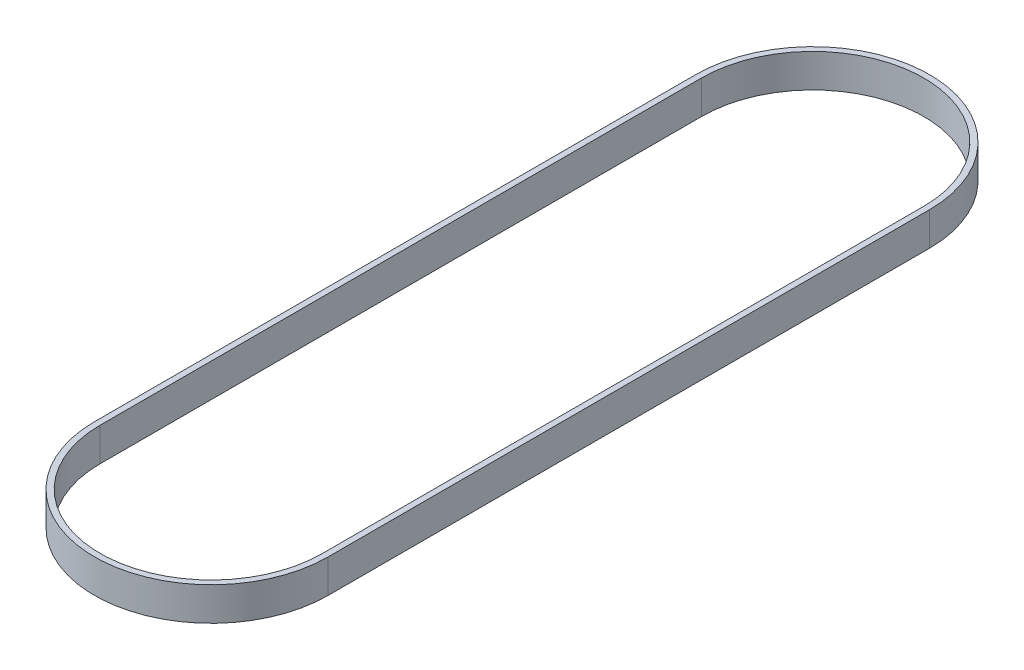
SolidWorks part; units mm, degrees
material "聚亚安酯(11671)"
ref_plane "前视基准面" through (0, 0, 0) normal (0, 0, 1) x (1, 0, 0)
ref_plane "上视基准面" through (0, 0, 0) normal (0, 1, 0) x (1, 0, 0)
ref_plane "右视基准面" through (0, 0, 0) normal (1, 0, 0) x (0, 0, -1)
sketch "草图1" plane through (0, 0, 0) normal (0, 1, 0) x (1, 0, 0)
  line L0 (0, -90) -> (0, 90) construction
  line L2 (-35, 90) -> (-35, -90)
  line L4 (35, 90) -> (35, -90)
  line L6 (-33.26, 90) -> (-33.26, -90)
  line L8 (33.26, -90) -> (33.26, 90)
  arc A0 (33.26, 90) -> (-33.26, 90) centre (0, 90) ccw
  arc A1 (-33.26, -90) -> (33.26, -90) centre (0, -90) ccw
  arc A3 (35, 90) -> (-35, 90) centre (0, 90) ccw
  arc A4 (-35, -90) -> (35, -90) centre (0, -90) ccw
  circle A5 centre (0, 90) radius 35 construction
  circle A6 centre (0, -90) radius 35 construction
  circle A9 centre (0, 90) radius 33.26 construction
  circle A10 centre (0, -90) radius 33.26 construction
  dimension "D1" = 66.52
  dimension "D2" = 180
  dimension "D5" = 1.74
  dimension "D6" = 1.74
extrude "凸台-拉伸1" add sketch "草图1" along normal blind 10
